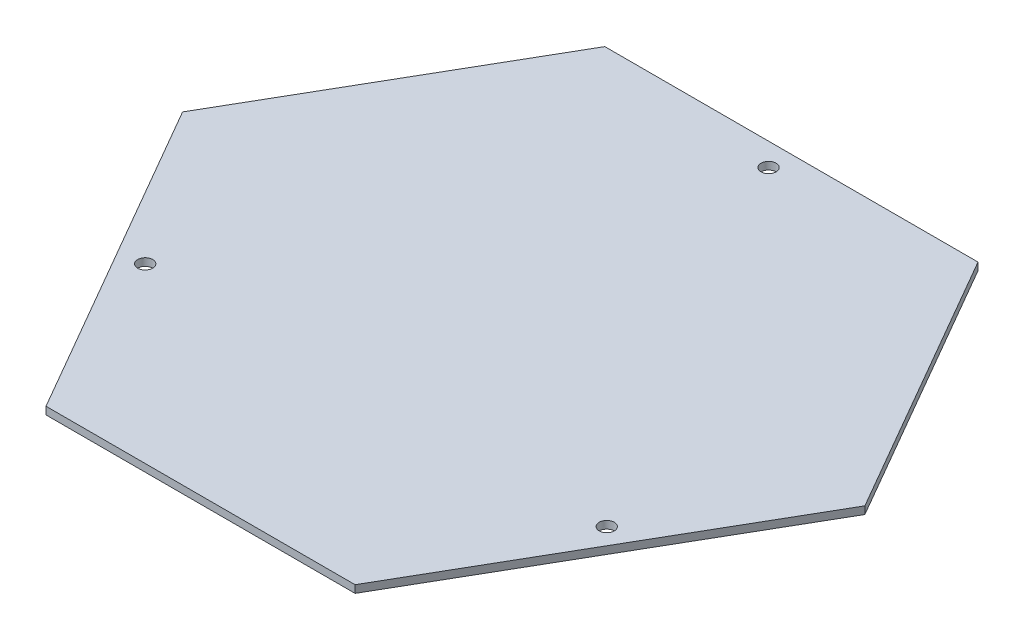
SolidWorks part; units mm, degrees
material "7075-T6, Plate (SS)"
ref_plane "Front Plane" through (0, 0, 0) normal (0, 0, 1) x (1, 0, 0)
ref_plane "Top Plane" through (0, 0, 0) normal (0, 1, 0) x (1, 0, 0)
ref_plane "Right Plane" through (0, 0, 0) normal (1, 0, 0) x (0, 0, -1)
sketch "Sketch2" plane through (0, 0, 0) normal (0, 1, 0) x (1, 0, 0)
  line L0 (0, 0) -> (205, 0)
  line L1 (0, 0) -> (-123.75, 214.3413)
  line L2 (-123.75, 214.3413) -> (-162.8411, 282.0491) construction
  line L3 (-123.75, 214.3413) -> (-21.25, 391.8765)
  line L4 (205, 0) -> (328.75, 214.3413)
  line L5 (328.75, 214.3413) -> (398.1022, 334.4629) construction
  line L6 (328.75, 214.3413) -> (226.25, 391.8765)
  line L7 (-21.25, 391.8765) -> (226.25, 391.8765)
  dimension "D1" = 247.5
  dimension "D2" = 205
  dimension "D3" = 247.5
  dimension "D4" = 247.5
  dimension "D5" = 205
  dimension "D6" = 205
extrude "Boss-Extrude2" add sketch "Sketch2" along normal blind 5
sketch "Sketch3" plane through (0, 5, 0) normal (0, 1, 0) x (1, 0, 0)
  line L0 (-30, 376.7211) -> (235, 376.7211)
  line L1 (-21.25, 391.8765) -> (-123.75, 214.3413) construction
  line L2 (328.75, 214.3413) -> (226.25, 391.8765) construction
  line L4 (0, 0) -> (205, 0) construction
  line L5 (192.5568, 0) -> (317.6086, 233.6387)
  line L6 (-61.875, 107.1706) -> (-48.8846, 114.6706)
  line L7 (-123.75, 214.3413) -> (0, 0) construction
  circle A0 centre (102.5, 376.7211) radius 5
  circle A2 centre (255.0827, 116.8194) radius 5
  circle A3 centre (-48.8846, 114.6706) radius 5
  dimension "D1" = 10
  dimension "D6" = 10
  dimension "D3" = 10
  dimension "D2" = 265
  dimension "D5" = 265
extrude "Cut-Extrude3" cut sketch "Sketch3" against normal blind 10 contours A3 | A0 | A2
